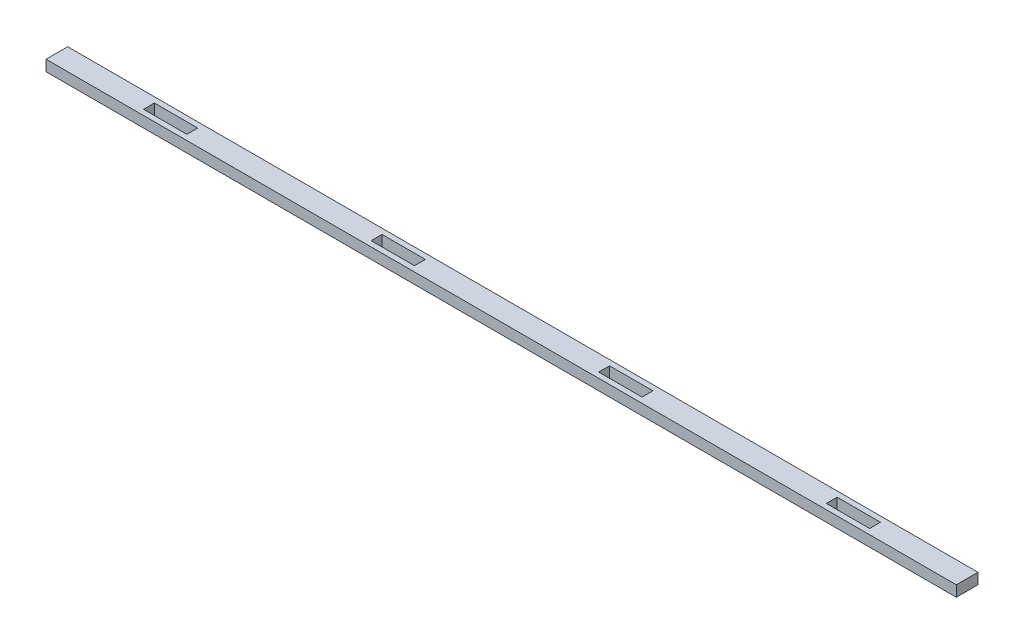
SolidWorks part; units mm, degrees
material "Cedar"
ref_plane "Front Plane" through (0, 0, 0) normal (0, 0, 1) x (1, 0, 0)
ref_plane "Top Plane" through (0, 0, 0) normal (0, 1, 0) x (1, 0, 0)
ref_plane "Right Plane" through (0, 0, 0) normal (1, 0, 0) x (0, 0, -1)
sketch "Sketch1" plane through (0, 0, 0) normal (0, 1, 0) x (1, 0, 0)
  line L1 (-266.7, 6.35) -> (266.7, 6.35)
  line L2 (-266.7, 6.35) -> (-266.7, -6.35)
  line L3 (-266.7, -6.35) -> (266.7, -6.35)
  line L4 (266.7, 6.35) -> (266.7, -6.35)
  line L5 (-266.7, 6.35) -> (266.7, -6.35) construction
  line L6 (-266.7, -6.35) -> (266.7, 6.35) construction
  point P0 (0, 0)
  dimension "D1" = 533.4
  dimension "D2" = 12.7
extrude "Boss-Extrude1" add sketch "Sketch1" along normal blind 6.35
sketch "Sketch2" plane through (0, 6.35, 0) normal (0, 1, 0) x (1, 0, 0)
  line L0 (-266.7, 0) -> (-212.725, 0) construction
  line L1 (-212.725, 3.175) -> (-187.325, 3.175)
  line L2 (-212.725, 3.175) -> (-212.725, -3.175)
  line L3 (-212.725, -3.175) -> (-187.325, -3.175)
  line L4 (-187.325, 3.175) -> (-187.325, -3.175)
  line L5 (-212.725, 3.175) -> (-187.325, -3.175) construction
  line L6 (-212.725, -3.175) -> (-187.325, 3.175) construction
  line L7 (-266.7, 6.35) -> (-266.7, -6.35) construction
  point P0 (-200.025, 0)
  dimension "D1" = 25.4
  dimension "D2" = 6.35
  dimension "D3" = 53.975
extrude "Cut-Extrude1" cut sketch "Sketch2" against normal through all
pattern_linear "LPattern1" count 4 spacing 133.35 along (1, 0, 0) of "Cut-Extrude1"
